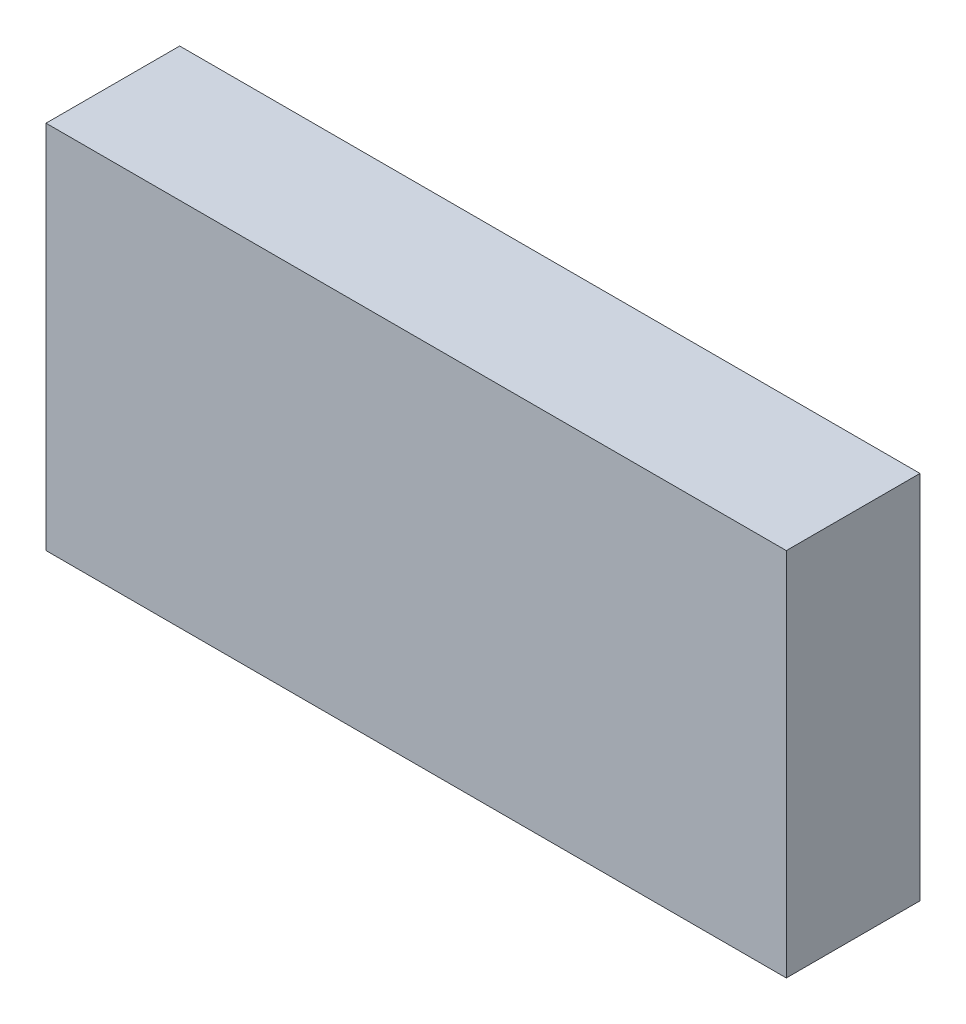
SolidWorks part; units mm, degrees
ref_plane "Alzado" through (0, 0, 0) normal (0, 0, 1) x (1, 0, 0)
ref_plane "Planta" through (0, 0, 0) normal (0, 1, 0) x (1, 0, 0)
ref_plane "Vista lateral" through (0, 0, 0) normal (1, 0, 0) x (0, 0, -1)
sketch "Croquis1" plane through (0, 0, 0) normal (0, 0, 1) x (1, 0, 0)
  line L1 (-36, 18) -> (36, 18)
  line L2 (-36, 18) -> (-36, -18)
  line L3 (-36, -18) -> (36, -18)
  line L4 (36, 18) -> (36, -18)
  line L5 (-36, 18) -> (36, -18) construction
  line L6 (-36, -18) -> (36, 18) construction
  point P0 (0, 0)
  dimension "D1" = 72
  dimension "D2" = 36
extrude "Saliente-Extruir1" add sketch "Croquis1" along normal blind 13
